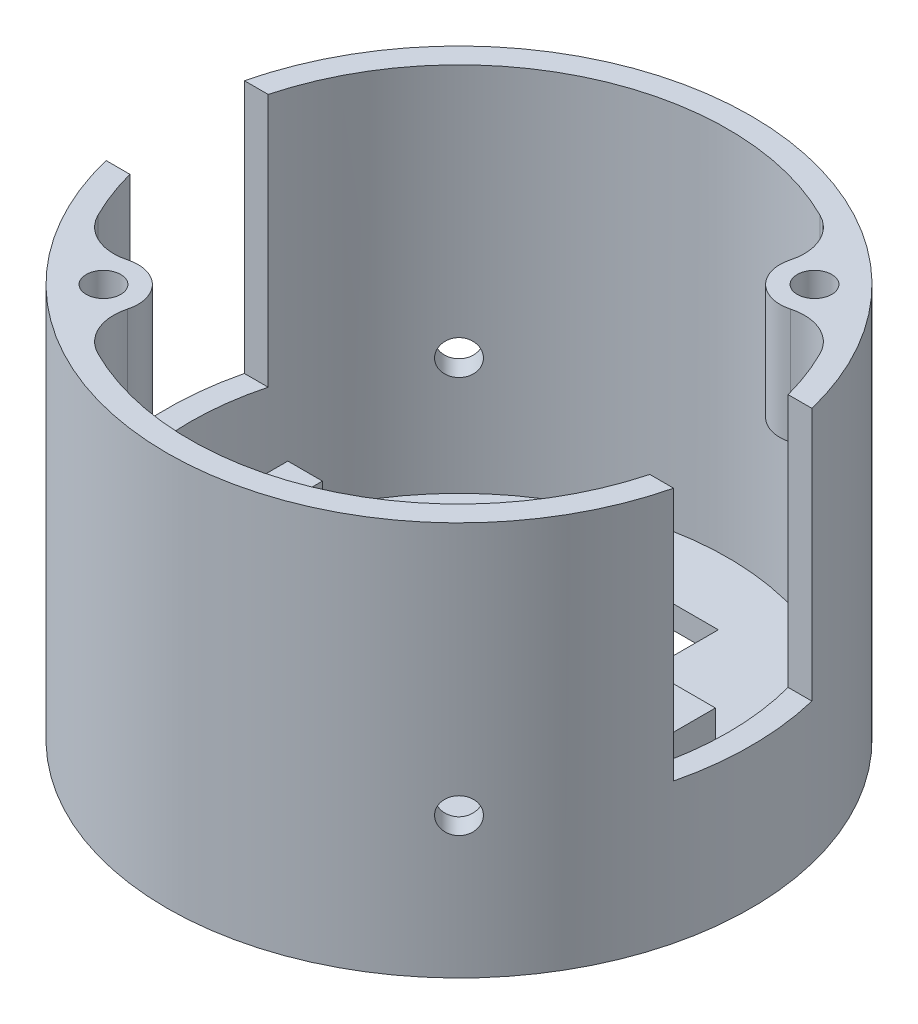
SolidWorks part; units mm, degrees
ref_plane "Front Plane" through (0, 0, 0) normal (0, 0, 1) x (1, 0, 0)
ref_plane "Top Plane" through (0, 0, 0) normal (0, 1, 0) x (1, 0, 0)
ref_plane "Right Plane" through (0, 0, 0) normal (1, 0, 0) x (0, 0, -1)
sketch "Sketch1" plane through (0, 0, 0) normal (0, 1, 0) x (1, 0, 0)
  circle A0 centre (0, 0) radius 25.34
  dimension "D1" = 50.68
extrude "Boss-Extrude1" add sketch "Sketch1" along normal blind 34.2
shell "Shell1" thickness 2
sketch "Sketch2" plane through (0, 34.2, 0) normal (0, 1, 0) x (1, 0, 0)
  line L0 (-42.4931, 0) -> (45.3167, 0) construction
  line L2 (25.34, 6) -> (-25.34, 6)
  line L3 (25.34, 6) -> (25.34, -6)
  line L4 (25.34, -6) -> (-25.34, -6)
  line L5 (-25.34, 6) -> (-25.34, -6)
  line L6 (25.34, 6) -> (-25.34, -6) construction
  line L7 (25.34, -6) -> (-25.34, 6) construction
  circle A0 centre (0, 0) radius 25.34 construction
  point P3 (0, 0)
  dimension "D1" = 12
extrude "Cut-Extrude1" cut sketch "Sketch2" against normal blind 22
sketch "Sketch3" plane through (0, 2, 0) normal (0, 1, 0) x (1, 0, 0)
  line L0 (-15.75, 0) -> (15.75, 0) construction
  line L1 (0, 31.0189) -> (0, -32.0406) construction
  line L2 (15.75, 6.5) -> (10.75, 6.5)
  line L3 (15.75, 6.5) -> (15.75, -6.5)
  line L4 (15.75, -6.5) -> (10.75, -6.5)
  line L5 (10.75, 6.5) -> (10.75, -6.5)
  line L6 (21.35, 6.5) -> (18.35, 6.5)
  line L7 (21.35, 6.5) -> (21.35, -6.5)
  line L8 (21.35, -6.5) -> (18.35, -6.5)
  line L9 (18.35, 6.5) -> (18.35, -6.5)
  line L10 (21.35, 6.5) -> (18.35, -6.5) construction
  line L11 (21.35, -6.5) -> (18.35, 6.5) construction
  line L12 (-21.35, -6.5) -> (-18.35, 6.5) construction
  line L13 (-21.35, 6.5) -> (-18.35, -6.5) construction
  line L14 (-18.35, 6.5) -> (-18.35, -6.5)
  line L15 (-21.35, -6.5) -> (-18.35, -6.5)
  line L16 (-21.35, 6.5) -> (-21.35, -6.5)
  line L17 (-21.35, 6.5) -> (-18.35, 6.5)
  line L18 (-15.75, -6.5) -> (-10.75, -6.5)
  line L19 (-10.75, 6.5) -> (-10.75, -6.5)
  line L20 (-15.75, 6.5) -> (-10.75, 6.5)
  line L21 (-15.75, 6.5) -> (-15.75, -6.5)
  point P3 (0, 0)
  point P8 (15.75, 0)
  point P9 (19.85, 0)
  point P20 (-19.85, 0)
  dimension "D1" = 31.5
  dimension "D2" = 13
  dimension "D3" = 5
  dimension "D4" = 3
  dimension "D5" = 2.6
extrude "Boss-Extrude2" add sketch "Sketch3" along normal blind 5
sketch "Sketch4" plane through (0, 34.2, 0) normal (0, 1, 0) x (1, 0, 0)
  line L0 (-15.4231, -15.4231) -> (15.4231, 15.4231) construction
  line L1 (-36.246, 0) -> (36.4607, 0) construction
  circle A0 centre (15.4231, 15.4231) radius 3
  circle A1 centre (15.4231, 15.4231) radius 1.5
  circle A2 centre (-15.4231, -15.4231) radius 3
  circle A3 centre (-15.4231, -15.4231) radius 1.5
  point P2 (0, 0)
  point P11 (13.3805, 13.3805)
  point P12 (0, 0)
  point P13 (0, 0)
  point P14 (15.4566, 15.4566)
  point P15 (15.4231, 15.4231)
  dimension "D2" = 3
  dimension "D3" = 6
  dimension "D1" = 45
  dimension "D4" = 43.6232
extrude "Boss-Extrude3" add sketch "Sketch4" against normal blind 10
fillet "Fillet1" radius 4 4 edges at (18.281, 29.2, -14.5107) (14.5107, 29.2, -18.281) (-18.281, 29.2, 14.5107) (-14.5107, 29.2, 18.281)
sketch "Sketch5" plane through (0, 34.2, 0) normal (0, 1, 0) x (1, 0, 0)
  line L0 (-41.8365, 0) -> (43.5087, 0) construction
  line L1 (-17.9181, 17.9181) -> (17.9181, -17.9181) construction
  arc A0 (24.6194, 6) -> (-24.6194, 6) centre (0, 0) ccw construction
  arc A1 (-24.6194, -6) -> (24.6194, -6) centre (0, 0) ccw construction
  point P10 (0, 0)
  dimension "D1" = 45
ref_plane "Plane1" through (17.9181, 34.2, 17.9181) normal (0.7071, 0, 0.7071) x (0.7071, 0, -0.7071)
sketch "Sketch6" plane through (17.9181, 34.2, 17.9181) normal (0.7071, 0, 0.7071) x (0.7071, 0, -0.7071)
  line L1 (-29.5829, 0) -> (30.7653, 0) construction
  circle A0 centre (0, -22) radius 1.5
  point P2 (1.3141, -24.3575)
  point P3 (0, -20.2262)
  dimension "D1" = 3
  dimension "D2" = 22
extrude "Cut-Extrude2" cut sketch "Sketch6" against normal through all
sketch "Sketch7" plane through (0, 2, 0) normal (0, 1, 0) x (1, 0, 0)
  line L0 (-39.6427, 0) -> (42.9579, 0) construction
  line L1 (5, 17.5) -> (-5, 17.5)
  line L2 (5, 17.5) -> (5, 12.5)
  line L3 (5, 12.5) -> (-5, 12.5)
  line L4 (-5, 17.5) -> (-5, 12.5)
  line L5 (5, 17.5) -> (-5, 12.5) construction
  line L6 (5, 12.5) -> (-5, 17.5) construction
  line L7 (5, -12.5) -> (-5, -17.5) construction
  line L8 (5, -17.5) -> (-5, -12.5) construction
  line L9 (5, -12.5) -> (-5, -12.5)
  line L10 (-5, -17.5) -> (-5, -12.5)
  line L11 (5, -17.5) -> (-5, -17.5)
  line L12 (5, -17.5) -> (5, -12.5)
  point P0 (0, 15)
  point P5 (0, -15)
  dimension "D1" = 5
  dimension "D2" = 10
  dimension "D3" = 15
extrude "Cut-Extrude3" cut sketch "Sketch7" against normal through all
